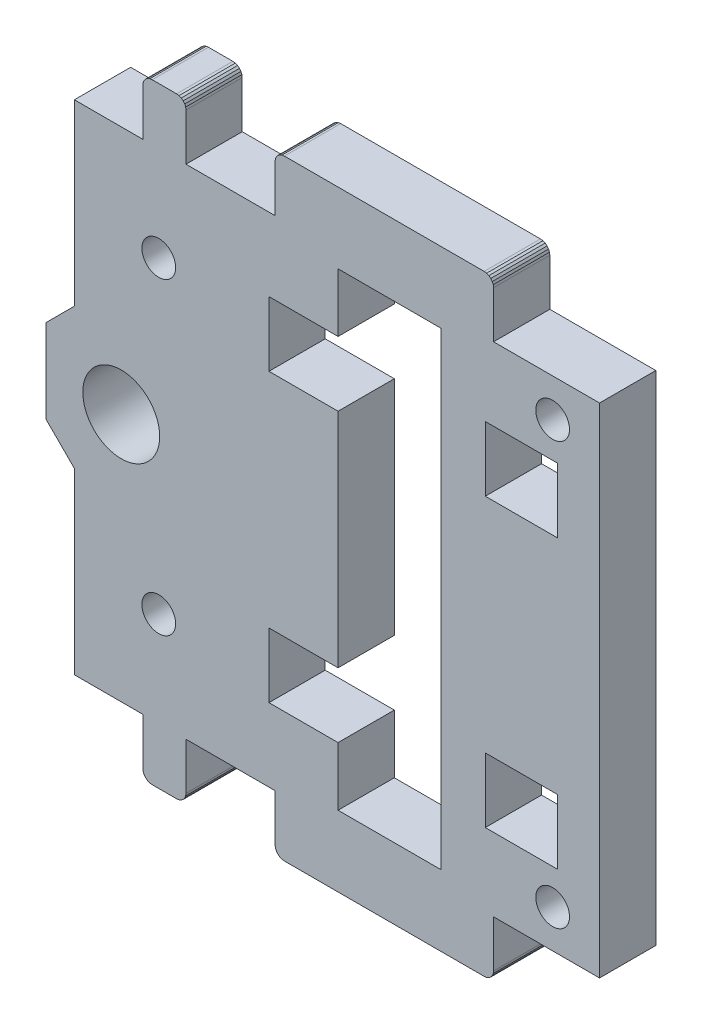
SolidWorks part; units mm, degrees
ref_plane "Plano frontal" through (0, 0, 0) normal (0, 0, 1) x (1, 0, 0)
ref_plane "Plano superior" through (0, 0, 0) normal (0, 1, 0) x (1, 0, 0)
ref_plane "Plano direito" through (0, 0, 0) normal (1, 0, 0) x (0, 0, -1)
sketch "Model" plane through (0, 0, 0) normal (0, 0, 1) x (1, 0, 0)
  line L0 (52.3834, 73.075) -> (52.2835, 72.8339)
  line L1 (38.1893, 9.2156) -> (38.2893, 8.9746)
  line L2 (38.2893, 8.9746) -> (38.4483, 8.7677)
  line L3 (38.4483, 8.7677) -> (38.6553, 8.6089)
  line L4 (27.8494, 36.536) -> (30.8494, 33.536)
  line L5 (27.8494, 45.5141) -> (27.8494, 41.0531)
  line L6 (27.8494, 45.5141) -> (30.8494, 48.5141)
  line L7 (30.8494, 48.5141) -> (30.8494, 67.575)
  line L8 (75.0494, 73.4411) -> (74.8082, 73.541)
  line L9 (75.5153, 72.8339) -> (75.4154, 73.075)
  line L10 (75.5494, 72.575) -> (75.5153, 72.8339)
  line L11 (38.8923, 73.541) -> (39.1512, 73.575)
  line L12 (39.1512, 73.575) -> (41.7508, 73.575)
  line L13 (38.6512, 73.4411) -> (38.8923, 73.541)
  line L14 (52.2494, 9.475) -> (52.2494, 14.475)
  line L15 (52.2494, 9.475) -> (52.2835, 9.2162)
  line L16 (53.2494, 73.575) -> (52.9906, 73.541)
  line L17 (52.9906, 73.541) -> (52.7494, 73.4411)
  line L18 (42.0097, 73.541) -> (41.7508, 73.575)
  line L19 (42.7153, 9.2162) -> (42.6154, 8.975)
  line L20 (42.6154, 8.975) -> (42.4565, 8.7679)
  line L21 (53.2494, 73.575) -> (74.5494, 73.575)
  line L22 (38.6553, 8.6089) -> (38.8964, 8.5091)
  line L23 (38.8964, 8.5091) -> (39.1551, 8.475)
  line L24 (74.8082, 73.541) -> (74.5494, 73.575)
  line L25 (42.6169, 73.075) -> (42.458, 73.2821)
  line L26 (42.458, 73.2821) -> (42.2508, 73.4411)
  line L27 (58.9669, 29.175) -> (58.9669, 52.875)
  line L28 (58.9669, 59.775) -> (58.9669, 66.025)
  line L29 (27.8457, 41.025) -> (27.8494, 40.997)
  line L30 (27.8494, 40.997) -> (27.8494, 36.536)
  line L31 (27.8494, 41.0531) -> (27.8457, 41.025)
  line L32 (30.8494, 14.475) -> (30.8494, 33.536)
  line L33 (30.8494, 14.475) -> (38.1512, 14.475)
  line L34 (86.8494, 14.475) -> (75.5494, 14.475)
  line L35 (75.5494, 14.475) -> (75.5494, 9.475)
  line L36 (42.7494, 14.475) -> (42.7494, 9.475)
  line L37 (86.8494, 67.575) -> (86.8494, 14.475)
  line L38 (86.8494, 67.575) -> (75.5494, 67.575)
  line L39 (51.5984, 59.775) -> (51.5984, 52.875)
  line L40 (51.5984, 52.875) -> (58.9669, 52.875)
  line L41 (74.6669, 59.775) -> (74.6669, 52.875)
  line L42 (82.3669, 59.775) -> (74.6669, 59.775)
  line L43 (74.6669, 52.875) -> (82.3669, 52.875)
  line L44 (82.3669, 52.875) -> (82.3669, 59.775)
  line L45 (58.9669, 29.175) -> (51.5984, 29.175)
  line L46 (74.6669, 29.175) -> (74.6669, 22.275)
  line L47 (51.5984, 22.275) -> (58.9669, 22.275)
  line L48 (51.5984, 29.175) -> (51.5984, 22.275)
  line L49 (82.3669, 22.275) -> (82.3669, 29.175)
  line L50 (74.6669, 22.275) -> (82.3669, 22.275)
  line L51 (82.3669, 29.175) -> (74.6669, 29.175)
  line L52 (42.7494, 9.475) -> (42.7153, 9.2162)
  line L53 (52.2835, 72.8339) -> (52.2494, 72.575)
  line L54 (38.444, 73.2821) -> (38.6512, 73.4411)
  line L55 (38.2851, 73.075) -> (38.444, 73.2821)
  line L56 (38.1852, 72.8339) -> (38.2851, 73.075)
  line L57 (42.7168, 72.8339) -> (42.6169, 73.075)
  line L58 (41.7494, 8.475) -> (39.1551, 8.475)
  line L59 (42.0082, 8.5091) -> (41.7494, 8.475)
  line L60 (75.4154, 73.075) -> (75.2565, 73.2821)
  line L61 (42.4565, 8.7679) -> (42.2494, 8.609)
  line L62 (42.2494, 8.609) -> (42.0082, 8.5091)
  line L63 (75.5494, 67.575) -> (75.5494, 72.575)
  line L64 (30.8494, 67.575) -> (38.1512, 67.575)
  line L65 (52.2494, 67.575) -> (52.2494, 72.575)
  line L66 (74.5494, 8.475) -> (53.2494, 8.475)
  line L67 (52.5423, 73.2821) -> (52.3834, 73.075)
  line L68 (42.7508, 72.575) -> (42.7168, 72.8339)
  line L69 (42.2508, 73.4411) -> (42.0097, 73.541)
  line L70 (69.9669, 16.0251) -> (58.9669, 16.0251)
  line L71 (69.9669, 66.025) -> (69.9669, 16.0251)
  line L72 (58.9669, 66.025) -> (69.9669, 66.025)
  line L73 (58.9669, 16.0251) -> (58.9669, 22.275)
  line L74 (58.9669, 59.775) -> (51.5984, 59.775)
  line L75 (52.7494, 8.609) -> (52.9906, 8.5091)
  line L76 (52.9906, 8.5091) -> (53.2494, 8.475)
  line L77 (74.5494, 8.475) -> (74.8082, 8.5091)
  line L78 (75.2565, 73.2821) -> (75.0494, 73.4411)
  line L79 (52.2835, 9.2162) -> (52.3834, 8.975)
  line L80 (52.3834, 8.975) -> (52.5423, 8.7679)
  line L81 (52.5423, 8.7679) -> (52.7494, 8.609)
  line L82 (74.8082, 8.5091) -> (75.0494, 8.609)
  line L83 (38.1551, 9.4743) -> (38.1893, 9.2156)
  line L84 (75.5153, 9.2162) -> (75.5494, 9.475)
  line L85 (75.0494, 8.609) -> (75.2565, 8.7679)
  line L86 (75.2565, 8.7679) -> (75.4154, 8.975)
  line L87 (52.7494, 73.4411) -> (52.5423, 73.2821)
  line L88 (38.1512, 72.575) -> (38.1852, 72.8339)
  line L89 (42.7508, 72.575) -> (42.7508, 67.575)
  line L90 (75.4154, 8.975) -> (75.5153, 9.2162)
  line L91 (38.1512, 67.575) -> (38.1512, 72.575)
  line L92 (42.7508, 67.575) -> (52.2494, 67.575)
  line L93 (38.1512, 14.475) -> (38.1551, 9.4743)
  line L94 (42.7494, 14.475) -> (52.2494, 14.475)
  circle A0 centre (81.8494, 18.525) radius 1.8
  circle A1 centre (39.8494, 24.575) radius 1.8
  circle A2 centre (35.8494, 41.025) radius 4.1
  circle A3 centre (39.8494, 57.475) radius 1.8
  circle A4 centre (81.8494, 63.525) radius 1.8
extrude "Ressalto-extrusão1" add sketch "Model" along normal blind 6
ref_plane "Plano2" through (0, 41.025, 0) normal (0, -1, 0) x (-1, 0, 0)
ref_plane "Plano3" through (0, 0, 3) normal (0, 0, 1) x (1, 0, 0)
ref_plane "Plano5" through (64.4669, 0, 0) normal (-1, 0, 0) x (0, 0, 1)
